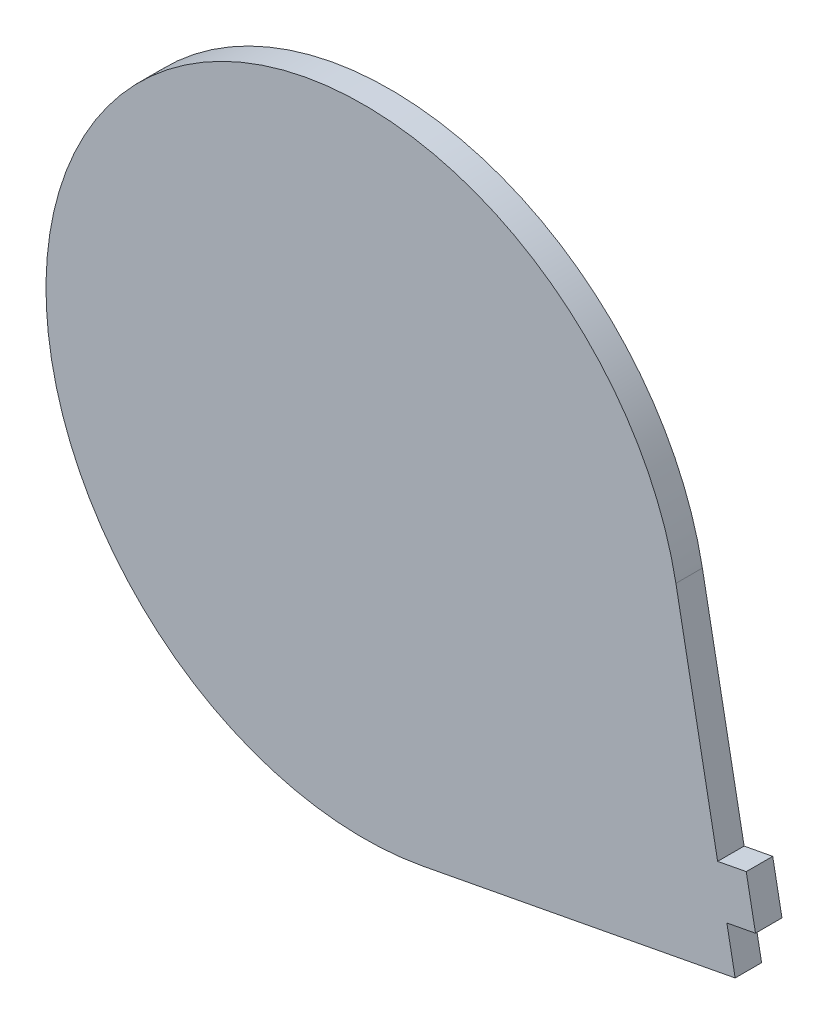
SolidWorks part; units mm, degrees
ref_plane "Front Plane" through (0, 0, 0) normal (0, 0, 1) x (1, 0, 0)
ref_plane "Top Plane" through (0, 0, 0) normal (0, 1, 0) x (1, 0, 0)
ref_plane "Right Plane" through (0, 0, 0) normal (1, 0, 0) x (0, 0, -1)
sketch "Sketch1" plane through (0, 0, 0) normal (0, 0, 1) x (1, 0, 0)
  line L0 (58.9481, 11.186) -> (66.8283, -30.3414)
  line L1 (70.1341, -47.762) -> (11.186, -58.9481)
  line L4 (66.8283, -30.3414) -> (72.2319, -29.316)
  line L5 (73.9777, -38.5158) -> (72.2319, -29.316)
  line L14 (73.9777, -38.5158) -> (68.5741, -39.5412)
  line L15 (68.5741, -39.5412) -> (70.1341, -47.762)
  arc A0 (58.9481, 11.186) -> (11.186, -58.9481) centre (0, 0) ccw
  point P9 (0, 0)
  dimension "D1" = 120
  dimension "D2" = 5.5
  dimension "D3" = 11.186
  dimension "D4" = 66.8283
  dimension "D5" = 68.5741
extrude "Boss-Extrude1" add sketch "Sketch1" along normal blind 5
